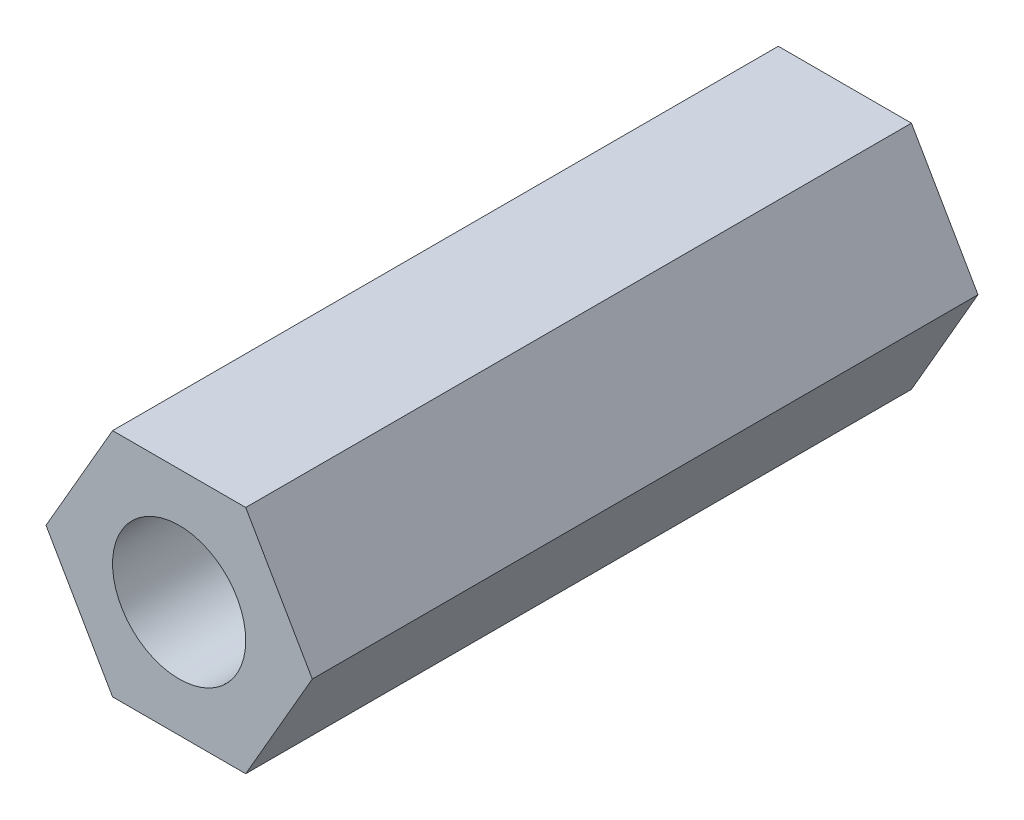
SolidWorks part; units mm, degrees
ref_plane "Alzado" through (0, 0, 0) normal (0, 0, 1) x (1, 0, 0)
ref_plane "Planta" through (0, 0, 0) normal (0, 1, 0) x (1, 0, 0)
ref_plane "Vista lateral" through (0, 0, 0) normal (1, 0, 0) x (0, 0, -1)
sketch "Croquis1" plane through (0, 0, 0) normal (0, 0, 1) x (1, 0, 0)
  line L0 (0, 0) -> (0.0003, 2.5981) construction
  line L1 (1.5003, 2.5979) -> (-1.4997, 2.5983)
  line L2 (-1.4997, 2.5983) -> (-3, 0.0004)
  line L3 (-3, 0.0004) -> (-1.5003, -2.5979)
  line L4 (-1.5003, -2.5979) -> (1.4997, -2.5983)
  line L5 (1.4997, -2.5983) -> (3, -0.0004)
  line L6 (3, -0.0004) -> (1.5003, 2.5979)
  circle A0 centre (0, 0) radius 2.5981 construction
  circle A1 centre (0, 0) radius 1.5
  dimension "D2" = 3
  dimension "D1" = 3
extrude "Saliente-Extruir1" add sketch "Croquis1" along normal blind 15
